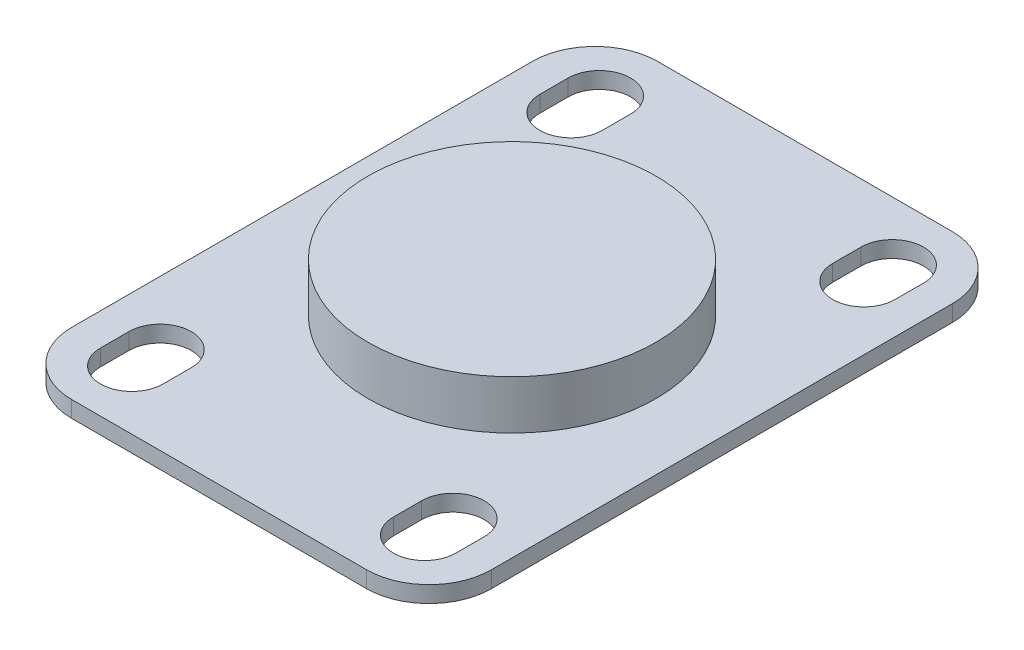
SolidWorks part; units mm, degrees
ref_plane "前视基准面" through (0, 0, 0) normal (0, 0, 1) x (1, 0, 0)
ref_plane "上视基准面" through (0, 0, 0) normal (0, 1, 0) x (1, 0, 0)
ref_plane "右视基准面" through (0, 0, 0) normal (1, 0, 0) x (0, 0, -1)
sketch "草图1" plane through (0, 0, 0) normal (0, 1, 0) x (1, 0, 0)
  line L0 (0, 0) -> (0, 47.6853) construction
  line L1 (-15.1, -30) -> (15.1, -30)
  line L2 (-21.5, -23.6) -> (-21.5, 23.6)
  line L3 (-15.1, 30) -> (15.1, 30)
  line L4 (21.5, -23.6) -> (21.5, 23.6)
  line L5 (-21.5, -30) -> (21.5, 30) construction
  line L6 (-21.5, 30) -> (21.5, -30) construction
  line L7 (0, 0) -> (47.9622, 0) construction
  line L8 (-18.2, 21.05) -> (-18.2, 23.95)
  line L9 (18.2, 23.95) -> (11.8, 21.05) construction
  line L10 (-11.8, 21.05) -> (-11.8, 23.95)
  line L11 (-18.2, 21.05) -> (-11.8, 23.95) construction
  line L12 (-18.2, 23.95) -> (-11.8, 21.05) construction
  line L13 (18.2, 21.05) -> (11.8, 23.95) construction
  line L14 (11.8, 21.05) -> (11.8, 23.95)
  line L15 (18.2, 21.05) -> (18.2, 23.95)
  line L16 (18.2, -21.05) -> (11.8, -23.95) construction
  line L17 (-18.2, -23.95) -> (-11.8, -21.05) construction
  line L18 (-18.2, -21.05) -> (-11.8, -23.95) construction
  line L19 (18.2, -23.95) -> (11.8, -21.05) construction
  line L20 (18.2, -21.05) -> (18.2, -23.95)
  line L21 (11.8, -21.05) -> (11.8, -23.95)
  line L22 (-11.8, -21.05) -> (-11.8, -23.95)
  line L23 (-18.2, -21.05) -> (-18.2, -23.95)
  line L24 (-15.1, -30) -> (15.1, -30)
  arc A0 (-18.2, 23.95) -> (-11.8, 23.95) centre (-15, 23.95) cw
  arc A1 (-18.2, 21.05) -> (-11.8, 21.05) centre (-15, 21.05) ccw
  arc A2 (18.2, 21.05) -> (11.8, 21.05) centre (15, 21.05) cw
  arc A3 (18.2, 23.95) -> (11.8, 23.95) centre (15, 23.95) ccw
  arc A4 (18.2, -23.95) -> (11.8, -23.95) centre (15, -23.95) cw
  arc A5 (18.2, -21.05) -> (11.8, -21.05) centre (15, -21.05) ccw
  arc A6 (-18.2, -21.05) -> (-11.8, -21.05) centre (-15, -21.05) cw
  arc A7 (-18.2, -23.95) -> (-11.8, -23.95) centre (-15, -23.95) ccw
  arc A8 (-21.5, -23.6) -> (-15.1, -30) centre (-15.1, -23.6) ccw
  arc A9 (15.1, -30) -> (21.5, -23.6) centre (15.1, -23.6) ccw
  arc A10 (21.5, 23.6) -> (15.1, 30) centre (15.1, 23.6) ccw
  arc A11 (-21.5, 23.6) -> (-15.1, 30) centre (-15.1, 23.6) cw
  point P0 (0, 0)
  point P6 (-15, 22.5)
  point P22 (15, 22.5)
  point P35 (15, -22.5)
  point P36 (-15, -22.5)
  dimension "D4" = 2.9
  dimension "D7" = 6.4
  dimension "D1" = 43
  dimension "D2" = 60
  dimension "D3" = 6.4
  dimension "D5" = 30
  dimension "D6" = 45
extrude "凸台-拉伸1" add sketch "草图1" along normal blind 1.68 contours A11 L2 A8 L1 A9 L4 A10 L3 A7 L23 A6 L22 A5 L20 A4 L21 A3 L15 A2 L14 A1 L8 A0 L10
sketch "草图2" plane through (0, 1.68, 0) normal (0, 1, 0) x (1, 0, 0)
  circle A0 centre (0, 0) radius 14.75
  dimension "D1" = 29.5
extrude "凸台-拉伸3" add sketch "草图2" along normal blind 5
